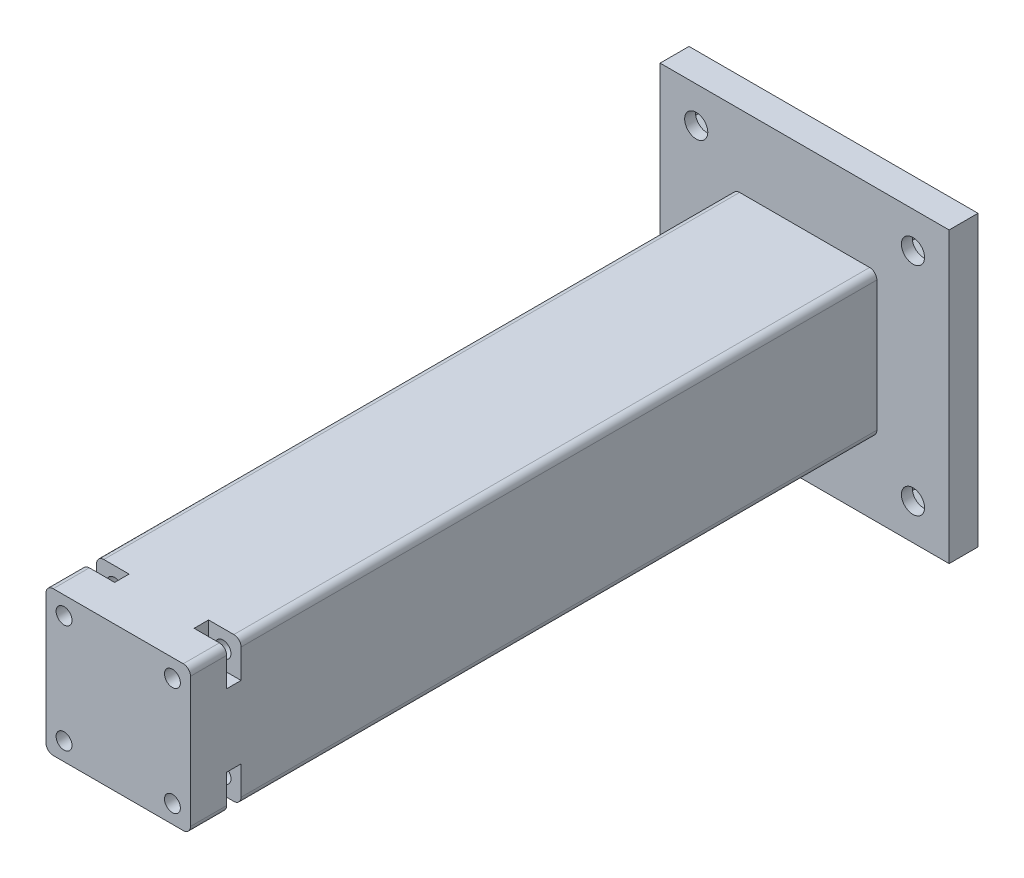
SolidWorks part; units mm, degrees
ref_plane "Plan de face" through (0, 0, 0) normal (0, 0, 1) x (1, 0, 0)
ref_plane "Plan de dessus" through (0, 0, 0) normal (0, 1, 0) x (1, 0, 0)
ref_plane "Plan de droite" through (0, 0, 0) normal (1, 0, 0) x (0, 0, -1)
sketch "Esquisse1" plane through (0, 0, 0) normal (0, 0, 1) x (1, 0, 0)
  line L1 (-20, 20) -> (20, 20)
  line L2 (-20, 20) -> (-20, -20)
  line L3 (-20, -20) -> (20, -20)
  line L4 (20, 20) -> (20, -20)
  dimension "D1" = 20
  dimension "D2" = 40
  dimension "D3" = 20
  dimension "D4" = 40
extrude "Boss.-Extru.1" add sketch "Esquisse1" along normal blind 4
sketch "Esquisse4" plane through (0, 0, 4) normal (0, 0, 1) x (1, 0, 0)
  line L1 (-10, 10) -> (10, 10)
  line L2 (-10, 10) -> (-10, -10)
  line L3 (-10, -10) -> (10, -10)
  line L4 (10, 10) -> (10, -10)
  point P4 (0, 0)
  dimension "D1" = 10
  dimension "D2" = 20
  dimension "D3" = 10
  dimension "D4" = 20
extrude "Boss.-Extru.4" add sketch "Esquisse4" along normal blind 95
fillet "Congé3" radius 1 4 edges at (-10, 10, 51.5) (10, 10, 51.5) (-10, -10, 51.5) (10, -10, 51.5)
sketch "Esquisse5" plane through (0, 0, 99) normal (0, 0, 1) x (1, 0, 0)
  line L0 (9, 10) -> (-9, 10) construction
  line L1 (-10, 9) -> (-10, -9) construction
  line L2 (10, -9) -> (10, 9) construction
  line L3 (-9, -10) -> (9, -10) construction
  circle A0 centre (7.5, 7.5) radius 1.1
  circle A1 centre (-7.5, 7.5) radius 1.1
  circle A2 centre (-7.5, -7.5) radius 1.1
  circle A3 centre (7.5, -7.5) radius 1.1
  dimension "D1" = 2.2
  dimension "D2" = 2.5
  dimension "D3" = 2.5
  dimension "D4" = 2.5
  dimension "D5" = 2.5
extrude "Enlèv. mat.-Extru.1" cut sketch "Esquisse5" against normal blind 20
sketch "Esquisse6" plane through (0, -10, 0) normal (0, -1, 0) x (1, 0, 0)
  line L0 (-9, 99) -> (9, 99) construction
  line L1 (-10, 94) -> (-5.5, 94)
  line L2 (-10, 94) -> (-10, 92)
  line L3 (-10, 92) -> (-5.5, 92)
  line L4 (-5.5, 94) -> (-5.5, 92)
  line L5 (10, 94) -> (5.5, 94)
  line L6 (10, 94) -> (10, 92)
  line L7 (10, 92) -> (5.5, 92)
  line L8 (5.5, 94) -> (5.5, 92)
  line L9 (-10, 4) -> (-10, 99) construction
  line L10 (10, 99) -> (10, 4) construction
  dimension "D2" = 5
  dimension "D3" = 2
  dimension "D5" = 4.5
  dimension "D6" = 4.5
extrude "Enlèv. mat.-Extru.2" cut sketch "Esquisse6" against normal blind 5
mirror "Symétrie1" about plane through (0, 0, 0) normal (0, 1, 0) of "Enlèv. mat.-Extru.2"
sketch "Esquisse7" plane through (0, 0, 0) normal (0, 0, -1) x (-1, 0, 0)
  line L0 (20, 20) -> (20, -20) construction
  line L1 (-20, -20) -> (-20, 20) construction
  line L2 (20, -20) -> (-20, -20) construction
  line L3 (-20, 20) -> (20, 20) construction
  line L4 (-9, 10) -> (9, 10) construction
  line L5 (10, 9) -> (10, -9) construction
  circle A0 centre (15, 15) radius 1.6
  circle A1 centre (15, -15) radius 1.6
  circle A2 centre (-15, -15) radius 1.6
  circle A3 centre (-15, 15) radius 1.6
  dimension "D1" = 3.2
  dimension "D2" = 5
  dimension "D3" = 5
  dimension "D4" = 5
  dimension "D5" = 5
  dimension "D6" = 5
  dimension "D7" = 5
extrude "Enlèv. mat.-Extru.3" cut sketch "Esquisse7" against normal up to surface (4 mm away) up to face at (0, 0, 4)
sketch "Esquisse8" plane through (0, 0, 0) normal (0, 0, -1) x (-1, 0, 0)
  line L0 (-20, -20) -> (-20, 20) construction
  line L1 (-11.9689, 13.25) -> (-11.9689, 16.75)
  line L2 (-11.9689, 16.75) -> (-15, 18.5)
  line L3 (-15, 18.5) -> (-18.0311, 16.75)
  line L4 (-18.0311, 16.75) -> (-18.0311, 13.25)
  line L5 (-18.0311, 13.25) -> (-15, 11.5)
  line L6 (-15, 11.5) -> (-11.9689, 13.25)
  line L7 (15, 11.5) -> (18.0311, 13.25)
  line L8 (18.0311, 13.25) -> (18.0311, 16.75)
  line L9 (18.0311, 16.75) -> (15, 18.5)
  line L10 (15, 18.5) -> (11.9689, 16.75)
  line L11 (11.9689, 16.75) -> (11.9689, 13.25)
  line L12 (11.9689, 13.25) -> (15, 11.5)
  line L13 (15, -18.5) -> (18.0311, -16.75)
  line L14 (18.0311, -16.75) -> (18.0311, -13.25)
  line L15 (18.0311, -13.25) -> (15, -11.5)
  line L16 (15, -11.5) -> (11.9689, -13.25)
  line L17 (11.9689, -13.25) -> (11.9689, -16.75)
  line L18 (11.9689, -16.75) -> (15, -18.5)
  line L19 (-11.9689, -16.75) -> (-11.9689, -13.25)
  line L20 (-11.9689, -13.25) -> (-15, -11.5)
  line L21 (-15, -11.5) -> (-18.0311, -13.25)
  line L22 (-18.0311, -13.25) -> (-18.0311, -16.75)
  line L23 (-18.0311, -16.75) -> (-15, -18.5)
  line L24 (-15, -18.5) -> (-11.9689, -16.75)
  line L25 (20, 20) -> (20, -20) construction
  circle A0 centre (-15, 15) radius 3.0311 construction
  circle A1 centre (15, 15) radius 3.0311 construction
  circle A2 centre (15, -15) radius 3.0311 construction
  circle A3 centre (-15, -15) radius 3.0311 construction
  dimension "D1" = 3.5
  dimension "D2" = 3.5
  dimension "D3" = 3.5
  dimension "D4" = 3.5
extrude "Enlèv. mat.-Extru.4" cut sketch "Esquisse8" against normal blind 2.5
